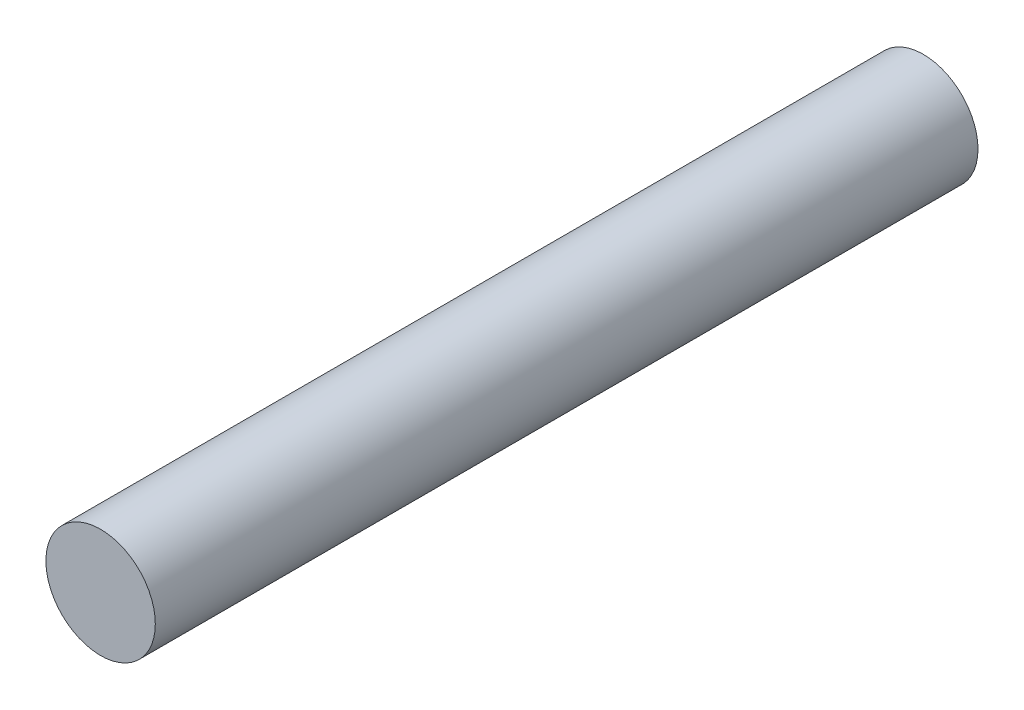
SolidWorks part; units mm, degrees
ref_plane "Front Plane" through (0, 0, 0) normal (0, 0, 1) x (1, 0, 0)
ref_plane "Top Plane" through (0, 0, 0) normal (0, 1, 0) x (1, 0, 0)
ref_plane "Right Plane" through (0, 0, 0) normal (1, 0, 0) x (0, 0, -1)
sketch "Sketch1" plane through (0, 0, 0) normal (0, 0, 1) x (1, 0, 0)
  circle A0 centre (-7.8047, 1.216) radius 3.99
  dimension "D1" = 7.98
extrude "Boss-Extrude1" add sketch "Sketch1" along normal blind 60
